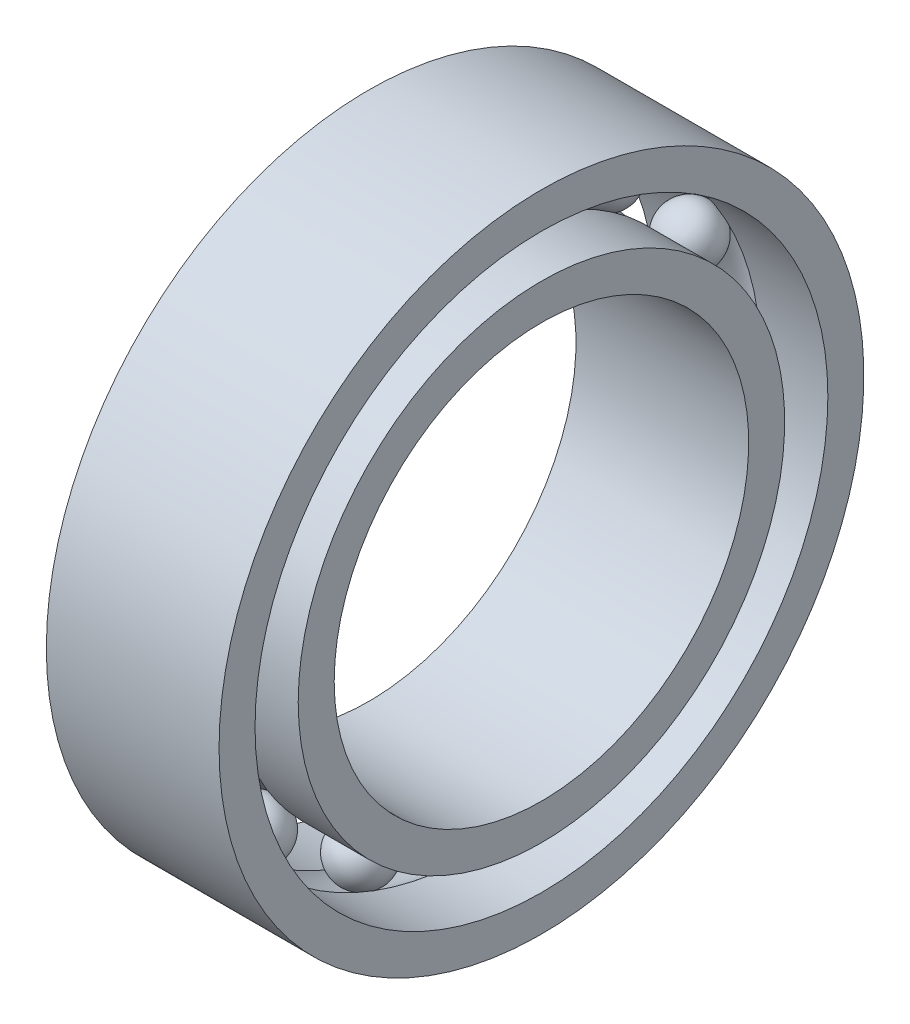
SolidWorks part; units mm, degrees
ref_plane "Front Plane" through (0, 0, 0) normal (0, 0, 1) x (1, 0, 0)
ref_plane "Top Plane" through (0, 0, 0) normal (0, 1, 0) x (1, 0, 0)
ref_plane "Right Plane" through (0, 0, 0) normal (1, 0, 0) x (0, 0, -1)
sketch "Sketch1" plane through (0, 0, 0) normal (0, 1, 0) x (1, 0, 0)
  line L0 (0, 28) -> (0, 18) construction
  line L1 (-7.5, 24.875) -> (-1.6536, 24.875)
  line L6 (-7.5, 24.875) -> (-7.5, 28)
  line L7 (-7.5, 28) -> (7.5, 28)
  line L8 (7.5, 24.875) -> (7.5, 28)
  line L9 (-7.5, 21.125) -> (-1.6536, 21.125)
  line L10 (-7.5, 21.125) -> (-7.5, 18)
  line L11 (-7.5, 18) -> (7.5, 18)
  line L12 (7.5, 21.125) -> (7.5, 18)
  line L13 (1.6536, 24.875) -> (7.5, 24.875)
  line L14 (1.6536, 21.125) -> (7.5, 21.125)
  line L15 (-1000, 0) -> (49000, 0) construction
  circle A0 centre (0, 23) radius 2.5
  circle A1 centre (0, 23) radius 2.5
  circle A2 centre (0, 23) radius 2.5
  circle A3 centre (0, 23) radius 2.5
  point P2 (0, 28)
  point P22 (0, 0)
  point P24 (0, 0)
  point P25 (0, 0)
  point P26 (0, 0)
  dimension "D4" = 3.125
  dimension "D2" = 18
  dimension "D1" = 28
  dimension "D3" = 15
  dimension "D5" = 3.75
revolve "Revolve2" add sketch "Sketch1" angle 360 about L15
sketch "Sketch2" plane through (0, 0, 0) normal (0, 1, 0) x (1, 0, 0)
  line L10 (-2.5, 23) -> (2.5, 23)
  circle A1 centre (0, 23) radius 2.5
  circle A2 centre (0, 23) radius 2.5
  circle A3 centre (0, 23) radius 2.5
  circle A4 centre (0, 23) radius 2.5
  circle A5 centre (0, 23) radius 2.5
  circle A6 centre (0, 23) radius 2.5
  circle A7 centre (0, 23) radius 2.5
  circle A8 centre (0, 23) radius 2.5
  dimension "D1" = 0
  dimension "D2" = 0
  dimension "D3" = 0
  dimension "D4" = 0
revolve "Revolve3" add sketch "Sketch2" angle 360 about L10
pattern_circular "CirPattern2" count 13 over 360 about axis through (0, 0, 0) along (1, 0, 0) of bodies 107
